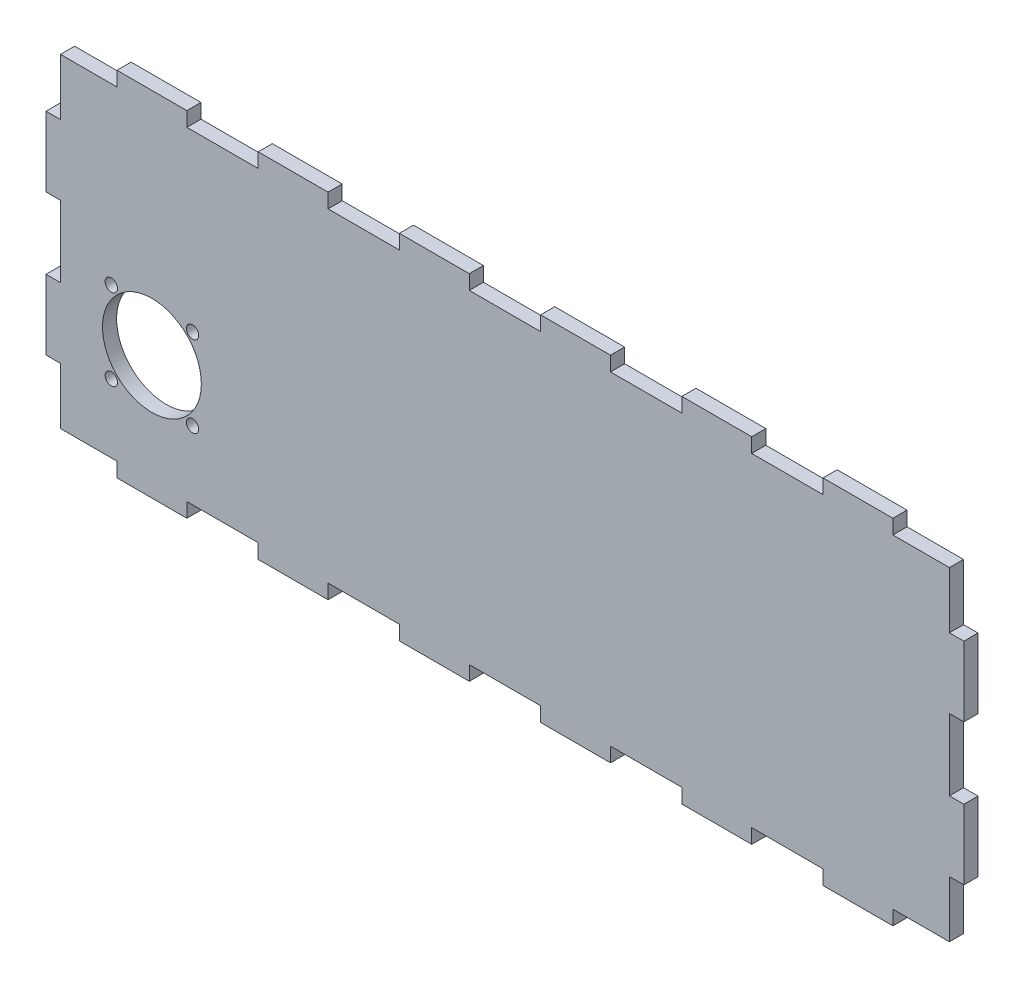
SolidWorks part; units mm, degrees
ref_plane "Front Plane" through (0, 0, 0) normal (0, 0, 1) x (1, 0, 0)
ref_plane "Top Plane" through (0, 0, 0) normal (0, 1, 0) x (1, 0, 0)
ref_plane "Right Plane" through (0, 0, 0) normal (1, 0, 0) x (0, 0, -1)
sketch "Sketch2" plane through (0, 0, 0) normal (0, 0, 1) x (1, 0, 0)
  line L1 (-130, 50) -> (130, 50)
  line L2 (-130, 50) -> (-130, -50)
  line L3 (-130, -50) -> (130, -50)
  line L4 (130, 50) -> (130, -50)
  line L5 (-130, 50) -> (130, -50) construction
  line L6 (-130, -50) -> (130, 50) construction
  point P0 (0, 0)
  dimension "D1" = 100
  dimension "D2" = 260
extrude "Boss-Extrude1" add sketch "Sketch2" along normal blind 4
sketch "Sketch3" plane through (0, 0, 4) normal (0, 0, 1) x (1, 0, 0)
  line L0 (-130, 50) -> (-130, -50) construction
  line L1 (-130, -29.9) -> (-125.9, -29.9)
  line L2 (-130, -29.9) -> (-130, -50.1)
  line L3 (-130, -50.1) -> (-125.9, -50.1)
  line L4 (-125.9, -29.9) -> (-125.9, -50.1)
  line L6 (-130, -50) -> (130, -50) construction
  dimension "D1" = 4.1
  dimension "D2" = 20.2
  dimension "D3" = 0.1
extrude "Cut-Extrude1" cut sketch "Sketch3" against normal blind 4
pattern_linear "LPattern1" count 3 spacing 40 along (0, 1, 0) of "Cut-Extrude1"
mirror "Mirror1" about plane through (0, 0, 0) normal (1, 0, 0) of "LPattern1", "Cut-Extrude1"
sketch "Sketch4" plane through (0, 0, 4) normal (0, 0, 1) x (1, 0, 0)
  line L0 (-125.9, -50) -> (125.9, -50) construction
  line L2 (-109.9, -50) -> (-130.1, -50)
  line L3 (-109.9, -50) -> (-109.9, -45.9)
  line L4 (-109.9, -45.9) -> (-130.1, -45.9)
  line L5 (-130.1, -50) -> (-130.1, -45.9)
  line L6 (-130, -10.1) -> (-130, -29.9) construction
  dimension "D1" = 20.2
  dimension "D2" = 0.1
  dimension "D3" = 4.1
extrude "Cut-Extrude2" cut sketch "Sketch4" against normal blind 4
pattern_linear "LPattern2" count 7 spacing 40 along (1, 0, 0) of "Cut-Extrude2"
mirror "Mirror2" about plane through (0, 0, 0) normal (0, 1, 0) of "LPattern2", "Cut-Extrude2"
sketch "Sketch5" plane through (0, 0, 4) normal (0, 0, 1) x (1, 0, 0)
  line L0 (-109.9, -50) -> (-90.1, -50) construction
  line L1 (-130, -10.1) -> (-130, -29.9) construction
  circle A0 centre (-100, -15) radius 14
  circle A1 centre (-111.5, -3.5) radius 1.75
  circle A2 centre (-88.5, -3.5) radius 1.75
  circle A3 centre (-111.5, -26.5) radius 1.75
  circle A4 centre (-88.5, -26.5) radius 1.75
  dimension "D1" = 3.5
  dimension "D2" = 3.5
  dimension "D3" = 3.5
  dimension "D4" = 3.5
  dimension "D5" = 28
  dimension "D6" = 35
  dimension "D7" = 30
  dimension "D8" = 23
  dimension "D9" = 23
  dimension "D10" = 23
  dimension "D11" = 11.5
  dimension "D12" = 11.5
  dimension "D13" = 11.5
  dimension "D14" = 11.5
  dimension "D15" = 11.5
extrude "Cut-Extrude3" cut sketch "Sketch5" against normal through all
